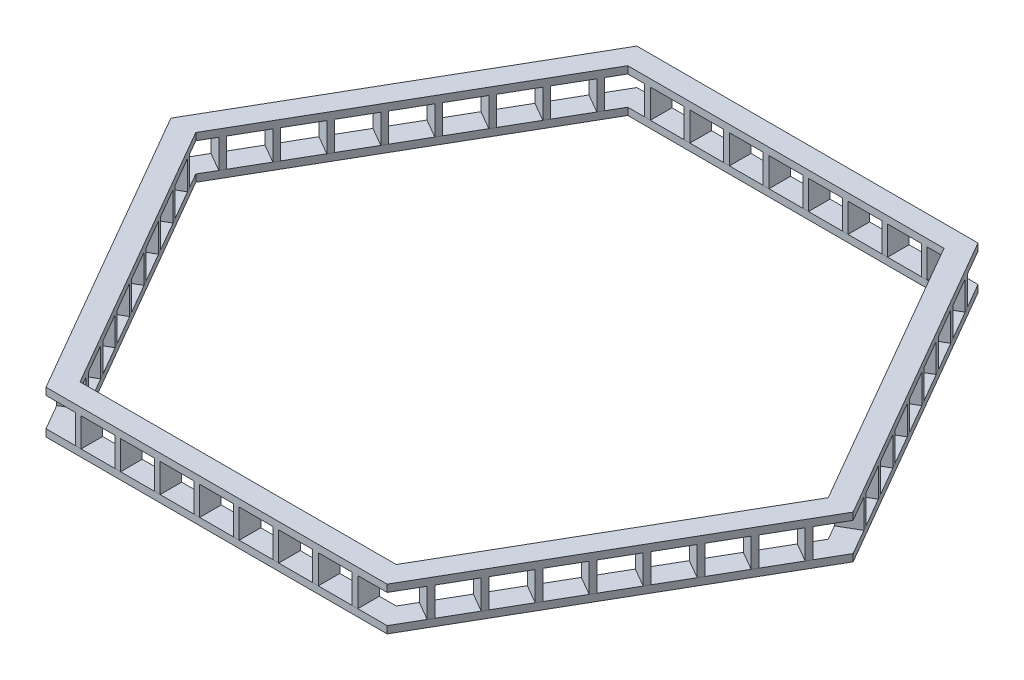
SolidWorks part; units mm, degrees
ref_plane "前视基准面" through (0, 0, 0) normal (0, 0, 1) x (1, 0, 0)
ref_plane "上视基准面" through (0, 0, 0) normal (0, 1, 0) x (1, 0, 0)
ref_plane "右视基准面" through (0, 0, 0) normal (1, 0, 0) x (0, 0, -1)
sketch "草图1" plane through (0, 0, 0) normal (0, 1, 0) x (1, 0, 0)
  line L0 (-1186.6025, -2055.2559) -> (1186.6025, -2055.2559)
  line L1 (-1100, -1905.2559) -> (1100, -1905.2559)
  line L2 (1100, -1905.2559) -> (2200, 0)
  line L3 (2200, 0) -> (1100, 1905.2559)
  line L4 (1100, 1905.2559) -> (-1100, 1905.2559)
  line L5 (-1100, 1905.2559) -> (-2200, 0)
  line L6 (-2200, 0) -> (-1100, -1905.2559)
  line L7 (1186.6025, -2055.2559) -> (2373.2051, 0)
  line L8 (2373.2051, 0) -> (1186.6025, 2055.2559)
  line L9 (1186.6025, 2055.2559) -> (-1186.6025, 2055.2559)
  line L10 (-1186.6025, 2055.2559) -> (-2373.2051, 0)
  line L11 (-2373.2051, 0) -> (-1186.6025, -2055.2559)
  circle A0 centre (0, 0) radius 1905.2559 construction
  dimension "D1" = 2200
  dimension "D2" = 150
extrude "凸台-拉伸2" add sketch "草图1" along normal blind 50
ref_plane "基准面2" through (0, 50, 0) normal (0, 1, 0) x (1, 0, 0)
sketch "草图2" plane through (0, 50, 0) normal (0, 1, 0) x (1, 0, 0)
  line L0 (0, 1905.2559) -> (0, 2055.2559) construction
  line L1 (1100, 1905.2559) -> (-1100, 1905.2559) construction
  line L2 (1186.6025, 2055.2559) -> (-1186.6025, 2055.2559) construction
  line L3 (-1100, 1905.2559) -> (-1100, 2055.2559) construction
  line L4 (1100, 1905.2559) -> (1100, 2055.2559) construction
  line L5 (0, 1905.2559) -> (-1100, 1905.2559) construction
  line L6 (-550, 1905.2559) -> (-550, 2055.2559) construction
  line L7 (-550, 2055.2559) -> (0, 2055.2559) construction
  line L8 (0, 1905.2559) -> (1100, 1905.2559) construction
  line L9 (550, 1905.2559) -> (550, 2055.2559) construction
  line L10 (0, 2055.2559) -> (550, 2055.2559) construction
  line L11 (550, 2055.2559) -> (1100, 2055.2559) construction
  line L12 (275, 2055.2559) -> (275, 1905.2559) construction
  line L13 (825, 2055.2559) -> (825, 1905.2559) construction
  line L14 (0, 2055.2559) -> (-550, 2055.2559) construction
  line L15 (-550, 2055.2559) -> (-1100, 2055.2559) construction
  line L16 (-825, 2055.2559) -> (-825, 1905.2559) construction
  line L17 (-275, 2055.2559) -> (-275, 1905.2559) construction
  line L18 (275, 2055.2559) -> (0, 2055.2559) construction
  line L19 (137.5, 2055.2559) -> (137.5, 1905.2559) construction
  line L20 (275, 2055.2559) -> (550, 2055.2559) construction
  line L21 (550, 2055.2559) -> (825, 2055.2559) construction
  line L22 (825, 2055.2559) -> (1100, 2055.2559) construction
  line L23 (412.5, 2055.2559) -> (412.5, 1905.2559) construction
  line L24 (687.5, 2055.2559) -> (687.5, 1905.2559) construction
  line L25 (962.5, 2055.2559) -> (962.5, 1905.2559) construction
  line L26 (0, 2055.2559) -> (-275, 2055.2559) construction
  line L27 (-275, 2055.2559) -> (-550, 2055.2559) construction
  line L28 (-550, 2055.2559) -> (-825, 2055.2559) construction
  line L29 (-825, 2055.2559) -> (-1100, 2055.2559) construction
  line L30 (-962.5, 2055.2559) -> (-962.5, 1905.2559) construction
  line L31 (-687.5, 2055.2559) -> (-687.5, 1905.2559) construction
  line L32 (-412.5, 2055.2559) -> (-412.5, 1905.2559) construction
  line L33 (-137.5, 2055.2559) -> (-137.5, 1905.2559) construction
  line L34 (117.5, 1905.2559) -> (117.5, 2055.2559)
  line L35 (117.5, 1905.2559) -> (157.5, 1905.2559)
  line L36 (117.5, 2055.2559) -> (157.5, 2055.2559)
  line L37 (157.5, 1905.2559) -> (157.5, 2055.2559)
  line L38 (117.5, 1905.2559) -> (157.5, 2055.2559) construction
  line L39 (117.5, 2055.2559) -> (157.5, 1905.2559) construction
  line L40 (432.5, 2055.2559) -> (392.5, 1905.2559) construction
  line L41 (432.5, 1905.2559) -> (392.5, 2055.2559) construction
  line L42 (432.5, 1905.2559) -> (392.5, 1905.2559)
  line L43 (432.5, 1905.2559) -> (432.5, 2055.2559)
  line L44 (432.5, 2055.2559) -> (392.5, 2055.2559)
  line L45 (392.5, 1905.2559) -> (392.5, 2055.2559)
  line L46 (667.5, 1905.2559) -> (707.5, 1905.2559)
  line L47 (667.5, 1905.2559) -> (707.5, 2055.2559) construction
  line L48 (667.5, 2055.2559) -> (707.5, 1905.2559) construction
  line L49 (667.5, 1905.2559) -> (667.5, 2055.2559)
  line L50 (707.5, 1905.2559) -> (707.5, 2055.2559)
  line L51 (667.5, 2055.2559) -> (707.5, 2055.2559)
  line L52 (982.5, 1905.2559) -> (942.5, 2055.2559) construction
  line L53 (982.5, 2055.2559) -> (942.5, 1905.2559) construction
  line L54 (982.5, 1905.2559) -> (942.5, 1905.2559)
  line L55 (982.5, 1905.2559) -> (982.5, 2055.2559)
  line L56 (982.5, 2055.2559) -> (942.5, 2055.2559)
  line L57 (942.5, 1905.2559) -> (942.5, 2055.2559)
  line L58 (-432.5, 1905.2559) -> (-432.5, 2055.2559)
  line L59 (-982.5, 2055.2559) -> (-942.5, 2055.2559)
  line L60 (-982.5, 1905.2559) -> (-942.5, 1905.2559)
  line L61 (-942.5, 1905.2559) -> (-942.5, 2055.2559)
  line L62 (-982.5, 1905.2559) -> (-982.5, 2055.2559)
  line L63 (-667.5, 1905.2559) -> (-707.5, 1905.2559)
  line L64 (-707.5, 1905.2559) -> (-707.5, 2055.2559)
  line L65 (-667.5, 2055.2559) -> (-707.5, 2055.2559)
  line L66 (-667.5, 1905.2559) -> (-667.5, 2055.2559)
  line L67 (-432.5, 1905.2559) -> (-392.5, 1905.2559)
  line L68 (-432.5, 2055.2559) -> (-392.5, 2055.2559)
  line L69 (-392.5, 1905.2559) -> (-392.5, 2055.2559)
  line L70 (-117.5, 1905.2559) -> (-157.5, 1905.2559)
  line L71 (-117.5, 1905.2559) -> (-117.5, 2055.2559)
  line L72 (-117.5, 2055.2559) -> (-157.5, 2055.2559)
  line L73 (-157.5, 1905.2559) -> (-157.5, 2055.2559)
  point P41 (137.5, 1980.2559)
  point P47 (137.5, 1980.2559)
  dimension "D1" = 40
extrude "凸台-拉伸3" add sketch "草图2" along normal blind 200 separate body
sketch "草图3" plane through (0, 0, 0) normal (0, 0, 1) x (1, 0, 0)
  line L0 (0, 0) -> (0, 600) construction
  dimension "D1" = 600
pattern_circular "阵列(圆周)2" count 6 every 60 about axis through (0, 0, 0) along (0, 1, 0) of bodies 171 169 173 174 172 108 168 170
ref_plane "基准面3" through (0, 250, 0) normal (0, 1, 0) x (1, 0, 0)
sketch "草图5" plane through (0, 250, 0) normal (0, 1, 0) x (1, 0, 0)
  line L0 (-2373.2051, 0) -> (-1186.6025, -2055.2559) construction
  line L1 (-2200, 0) -> (-1100, -1905.2559) construction
  line L2 (-1186.6025, -2055.2559) -> (1186.6025, -2055.2559) construction
  line L3 (-1100, -1905.2559) -> (1100, -1905.2559) construction
  line L4 (1100, -1905.2559) -> (2200, 0) construction
  line L5 (1186.6025, -2055.2559) -> (2373.2051, 0) construction
  line L6 (2373.2051, 0) -> (1186.6025, 2055.2559) construction
  line L7 (2200, 0) -> (1100, 1905.2559) construction
  line L8 (1100, 1905.2559) -> (-1100, 1905.2559) construction
  line L9 (1186.6025, 2055.2559) -> (-1186.6025, 2055.2559) construction
  line L10 (-1186.6025, 2055.2559) -> (-2373.2051, 0) construction
  line L11 (-1100, 1905.2559) -> (-2200, 0) construction
  line L12 (-2373.2051, 0) -> (-1186.6025, -2055.2559)
  line L13 (-2200, 0) -> (-1100, -1905.2559)
  line L14 (-1186.6025, -2055.2559) -> (1186.6025, -2055.2559)
  line L15 (-1100, -1905.2559) -> (1100, -1905.2559)
  line L16 (1100, -1905.2559) -> (2200, 0)
  line L17 (1186.6025, -2055.2559) -> (2373.2051, 0)
  line L18 (2373.2051, 0) -> (1186.6025, 2055.2559)
  line L19 (2200, 0) -> (1100, 1905.2559)
  line L20 (1100, 1905.2559) -> (-1100, 1905.2559)
  line L21 (1186.6025, 2055.2559) -> (-1186.6025, 2055.2559)
  line L22 (-1186.6025, 2055.2559) -> (-2373.2051, 0)
  line L23 (-1100, 1905.2559) -> (-2200, 0)
extrude "凸台-拉伸5" add sketch "草图5" along normal blind 50
